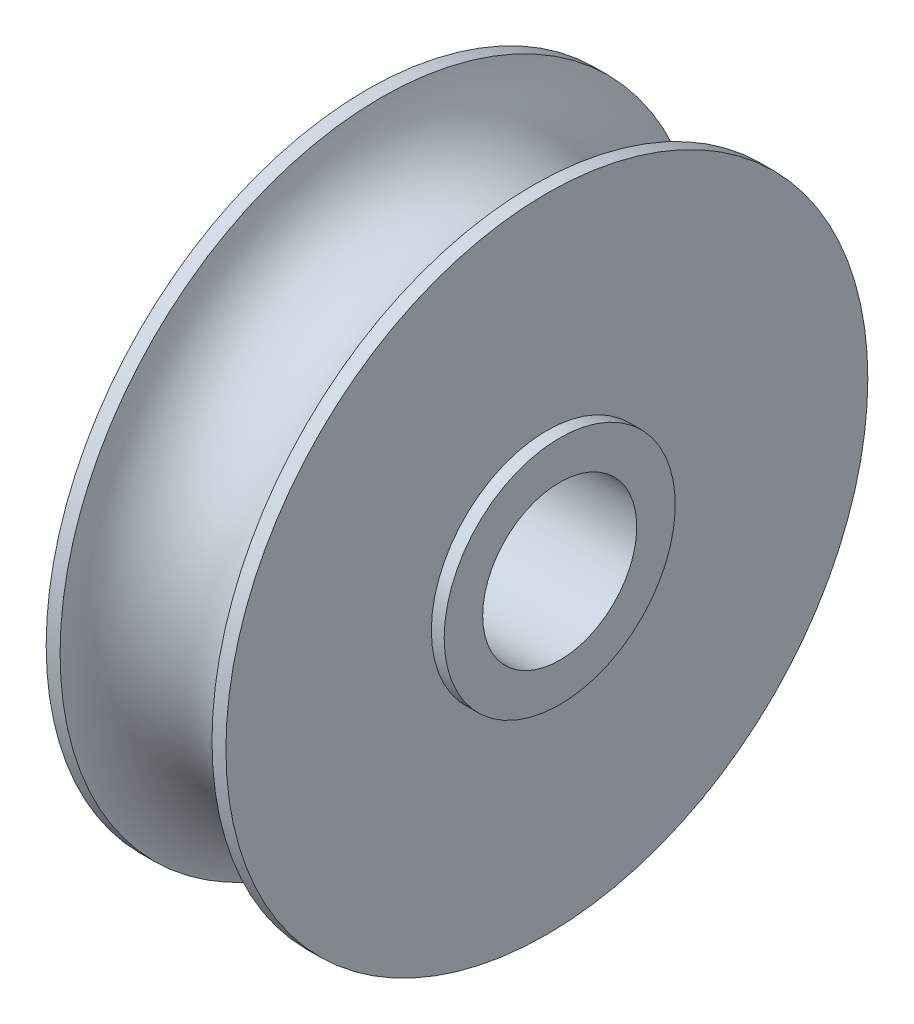
SolidWorks part; units mm, degrees
ref_plane "Plan de face" through (0, 0, 0) normal (0, 0, 1) x (1, 0, 0)
ref_plane "Plan de dessus" through (0, 0, 0) normal (0, 1, 0) x (1, 0, 0)
ref_plane "Plan de droite" through (0, 0, 0) normal (1, 0, 0) x (0, 0, -1)
sketch "Esquisse1" plane through (0, 0, 0) normal (0, 0, 1) x (1, 0, 0)
  line L0 (-29.0798, 0) -> (48.3718, 0) construction
  line L1 (0, -10.639) -> (0, 57.1667) construction
  line L2 (2.958, 12.5) -> (3.5, 12.5)
  line L3 (3.5, 12.5) -> (3.5, 4.5)
  line L4 (3.5, 4.5) -> (4, 4.5)
  line L5 (4, 4.5) -> (4, 3)
  line L6 (4, 3) -> (-4, 3)
  line L7 (-4, 4.5) -> (-4, 3)
  line L8 (-3.5, 4.5) -> (-4, 4.5)
  line L9 (-3.5, 12.5) -> (-3.5, 4.5)
  line L10 (-2.958, 12.5) -> (-3.5, 12.5)
  arc A0 (-2.958, 12.5) -> (2.958, 12.5) centre (0, 13) ccw
  point P14 (0, 3)
  dimension "D3" = 3
  dimension "D1" = 7
  dimension "D2" = 25
  dimension "D4" = 13
  dimension "D5" = 9
  dimension "D6" = 8
  dimension "D7" = 6
revolve "Révolution1" add sketch "Esquisse1" angle 360 about L0
